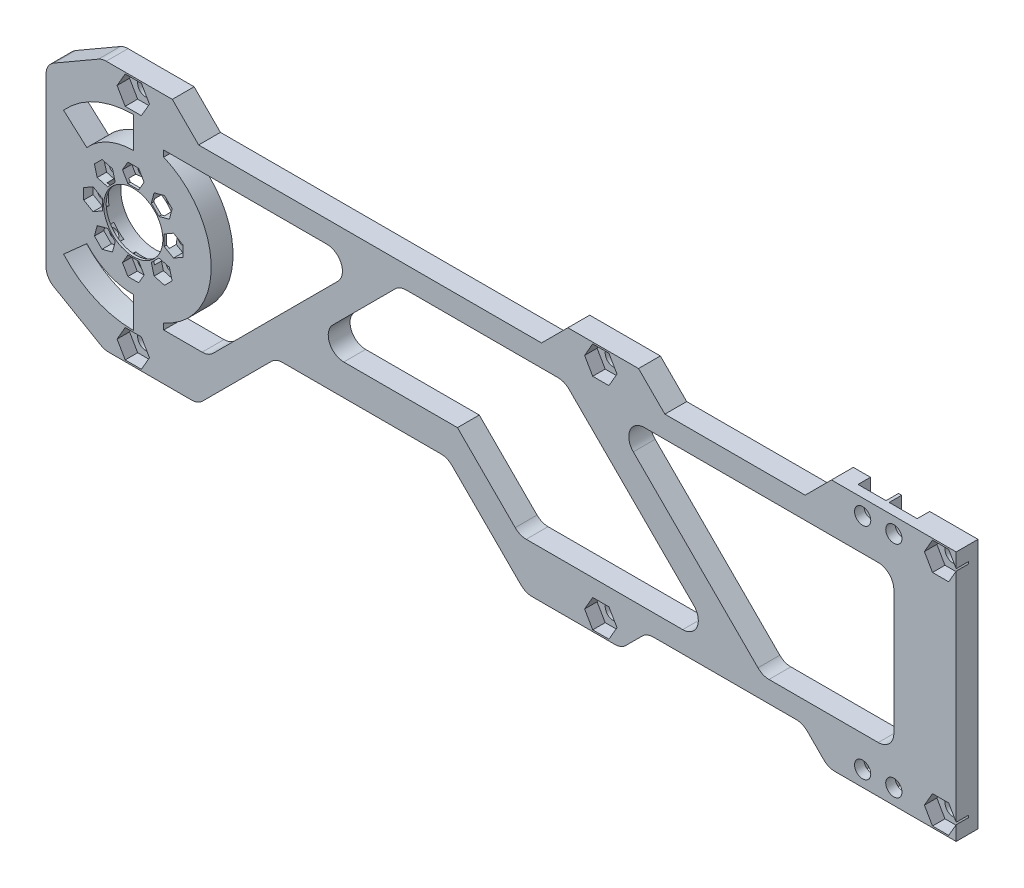
SolidWorks part; units mm, degrees
ref_plane "Front Plane" through (0, 0, 0) normal (0, 0, 1) x (1, 0, 0)
ref_plane "Top Plane" through (0, 0, 0) normal (0, 1, 0) x (1, 0, 0)
ref_plane "Right Plane" through (0, 0, 0) normal (1, 0, 0) x (0, 0, -1)
sketch "Sketch1" plane through (0, 0, 0) normal (0, 0, 1) x (1, 0, 0)
  line L0 (0, 0) -> (-274, 0)
  line L1 (-274, 0) -> (-299.9808, -15)
  line L2 (-299.9808, -15) -> (-299.9808, -65)
  line L3 (-299.9808, -65) -> (-273.2207, -80.4499)
  line L4 (-273.2207, -80.4499) -> (-243.2207, -80.4499)
  line L5 (-243.2207, -80.4499) -> (-218.1891, -55.4184)
  line L6 (-218.1891, -55.4184) -> (-163.1891, -55.4184)
  line L7 (-163.1891, -55.4184) -> (-138.1575, -80.4499)
  line L8 (-138.1575, -80.4499) -> (0, -80.4499)
  line L9 (0, -80.4499) -> (0, 0)
  dimension "D1" = 274
  dimension "D2" = 30
  dimension "D3" = 30
  dimension "D4" = 50
  dimension "D5" = 60
  dimension "D6" = 30
  dimension "D7" = 45
  dimension "D8" = 35.4
  dimension "D9" = 55
  dimension "D10" = 35.4
  dimension "D11" = 45
extrude "Boss-Extrude1" add sketch "Sketch1" along normal blind 7
sketch "Sketch2" plane through (0, 0, 7) normal (0, 0, 1) x (1, 0, 0)
  line L0 (-299.9808, -15) -> (-299.9808, -65) construction
  line L1 (-273.2207, -80.4499) -> (-243.2207, -80.4499) construction
  circle A0 centre (-263.9808, -40.4499) radius 9.5
  dimension "D1" = 36
  dimension "D2" = 40
  dimension "D3" = 19
extrude "Cut-Extrude1" cut sketch "Sketch2" against normal blind 7
sketch "Sketch3" plane through (0, 0, 7) normal (0, 0, 1) x (1, 0, 0)
  line L0 (-299.9808, -15) -> (-299.9808, -65) construction
  line L1 (-273.2207, -80.4499) -> (-243.2207, -80.4499) construction
  line L2 (0, -80.4499) -> (0, 0) construction
  line L3 (0, -40.225) -> (-214.1536, -40.225) construction
  circle A0 centre (-263.9808, -75.4499) radius 2.6
  circle A1 centre (-114, -75.4499) radius 2.6
  circle A2 centre (-30, -75.4499) radius 2.6
  circle A3 centre (-20, -75.4499) radius 2.6
  circle A4 centre (-5, -75.4499) radius 2.6
  circle A5 centre (-5, -5) radius 2.6
  circle A6 centre (-20, -5) radius 2.6
  circle A7 centre (-30, -5) radius 2.6
  circle A8 centre (-114, -5) radius 2.6
  circle A9 centre (-263.9808, -5) radius 2.6
  dimension "D1" = 5.2
  dimension "D2" = 36
  dimension "D3" = 5
  dimension "D4" = 5.2
  dimension "D5" = 5.2
  dimension "D6" = 5.2
  dimension "D7" = 5.2
  dimension "D8" = 114
  dimension "D9" = 10
  dimension "D10" = 20
  dimension "D11" = 5
extrude "Cut-Extrude2" cut sketch "Sketch3" against normal blind 7
sketch "Sketch5" plane through (0, 0, 0) normal (0, 0, -1) x (-1, 0, 0)
  line L0 (0, 0) -> (274, 0) construction
  line L2 (15.5, -5) -> (15.5, 0)
  line L3 (15.5, 0) -> (24.5, 0)
  line L4 (24.5, -5) -> (24.5, 0)
  line L5 (0, -40.225) -> (42.8271, -40.225) construction
  line L7 (25.5, -5) -> (25.5, 0)
  line L8 (25.5, 0) -> (34.5, 0)
  line L9 (34.5, -5) -> (34.5, 0)
  line L10 (0, -80.4499) -> (0, 0) construction
  line L11 (34.5, -75.4499) -> (34.5, -80.4499)
  line L12 (25.5, -80.4499) -> (34.5, -80.4499)
  line L13 (25.5, -75.4499) -> (25.5, -80.4499)
  line L14 (24.5, -75.4499) -> (24.5, -80.4499)
  line L15 (15.5, -80.4499) -> (24.5, -80.4499)
  line L16 (15.5, -75.4499) -> (15.5, -80.4499)
  arc A0 (15.5, -5) -> (24.5, -5) centre (20, -5) ccw
  arc A1 (25.5, -5) -> (34.5, -5) centre (30, -5) ccw
  arc A2 (25.5, -75.4499) -> (34.5, -75.4499) centre (30, -75.4499) cw
  arc A3 (15.5, -75.4499) -> (24.5, -75.4499) centre (20, -75.4499) cw
  dimension "D1" = 9
  dimension "D2" = 9
extrude "Cut-Extrude4" cut sketch "Sketch5" against normal blind 4
sketch "Sketch6" plane through (0, 0, 0) normal (0, 0, -1) x (-1, 0, 0)
  circle A0 centre (263.9808, -27.5499) radius 1.5
  circle A1 centre (263.9808, -40.4499) radius 9.5 construction
  circle A2 centre (273.1024, -31.3283) radius 1.5
  circle A3 centre (276.8808, -40.4499) radius 1.5
  circle A4 centre (273.1024, -49.5716) radius 1.5
  circle A5 centre (263.9808, -53.3499) radius 1.5
  circle A6 centre (254.8591, -49.5716) radius 1.5
  circle A7 centre (251.0808, -40.4499) radius 1.5
  circle A8 centre (254.8591, -31.3283) radius 1.5
  point P21 (263.9808, -40.4499)
  dimension "D1" = 12.9
  dimension "D2" = 3
  dimension "D3" = 8
extrude "Cut-Extrude5" cut sketch "Sketch6" against normal through all
sketch "Sketch8" plane through (0, 0, 0) normal (0, 0, -1) x (-1, 0, 0)
  circle A0 centre (263.9808, -40.4499) radius 11
  dimension "D1" = 22
extrude "Cut-Extrude8" cut sketch "Sketch8" against normal blind 6.2
sketch "Sketch10" plane through (0, 0, 7) normal (0, 0, 1) x (1, 0, 0)
  line L0 (0, -40.225) -> (-64.7485, -40.225) construction
  line L1 (-258.7846, -5) -> (-261.3827, -0.5)
  line L2 (-261.3827, -0.5) -> (-266.5788, -0.5)
  line L3 (-266.5788, -0.5) -> (-269.1769, -5)
  line L4 (-269.1769, -5) -> (-266.5788, -9.5)
  line L5 (-266.5788, -9.5) -> (-261.3827, -9.5)
  line L6 (-261.3827, -9.5) -> (-258.7846, -5)
  line L7 (-108.8038, -5) -> (-111.4019, -0.5)
  line L8 (-111.4019, -0.5) -> (-116.5981, -0.5)
  line L9 (-116.5981, -0.5) -> (-119.1962, -5)
  line L10 (-119.1962, -5) -> (-116.5981, -9.5)
  line L11 (-116.5981, -9.5) -> (-111.4019, -9.5)
  line L12 (-111.4019, -9.5) -> (-108.8038, -5)
  line L13 (0.1962, -5) -> (-2.4019, -0.5)
  line L14 (-2.4019, -0.5) -> (-7.5981, -0.5)
  line L15 (-7.5981, -0.5) -> (-10.1962, -5)
  line L16 (-10.1962, -5) -> (-7.5981, -9.5)
  line L17 (-7.5981, -9.5) -> (-2.4019, -9.5)
  line L18 (-2.4019, -9.5) -> (0.1962, -5)
  line L19 (0, -80.4499) -> (0, 0) construction
  line L20 (-2.4019, -70.9499) -> (0.1962, -75.4499)
  line L21 (-7.5981, -70.9499) -> (-2.4019, -70.9499)
  line L22 (-10.1962, -75.4499) -> (-7.5981, -70.9499)
  line L23 (-7.5981, -79.9499) -> (-10.1962, -75.4499)
  line L24 (-2.4019, -79.9499) -> (-7.5981, -79.9499)
  line L25 (0.1962, -75.4499) -> (-2.4019, -79.9499)
  line L26 (-111.4019, -70.9499) -> (-108.8038, -75.4499)
  line L27 (-116.5981, -70.9499) -> (-111.4019, -70.9499)
  line L28 (-119.1962, -75.4499) -> (-116.5981, -70.9499)
  line L29 (-116.5981, -79.9499) -> (-119.1962, -75.4499)
  line L30 (-111.4019, -79.9499) -> (-116.5981, -79.9499)
  line L31 (-108.8038, -75.4499) -> (-111.4019, -79.9499)
  line L32 (-261.3827, -70.9499) -> (-258.7846, -75.4499)
  line L33 (-266.5788, -70.9499) -> (-261.3827, -70.9499)
  line L34 (-269.1769, -75.4499) -> (-266.5788, -70.9499)
  line L35 (-266.5788, -79.9499) -> (-269.1769, -75.4499)
  line L36 (-261.3827, -79.9499) -> (-266.5788, -79.9499)
  line L37 (-258.7846, -75.4499) -> (-261.3827, -79.9499)
  circle A0 centre (-263.9808, -5) radius 4.5 construction
  circle A1 centre (-114, -5) radius 4.5 construction
  circle A2 centre (-5, -5) radius 4.5 construction
  circle A3 centre (-5, -75.4499) radius 4.5 construction
  circle A4 centre (-114, -75.4499) radius 4.5 construction
  circle A5 centre (-263.9808, -75.4499) radius 4.5 construction
  dimension "D1" = 9
  dimension "D2" = 9
  dimension "D3" = 9
extrude "Cut-Extrude10" cut sketch "Sketch10" against normal blind 4
sketch "Sketch11" plane through (0, 0, 7) normal (0, 0, 1) x (1, 0, 0)
  line L0 (-252.4096, -33.7778) -> (-251.513, -30.4317)
  line L1 (-260.5167, -27.5499) -> (-262.2487, -24.5499)
  line L2 (-262.2487, -24.5499) -> (-265.7128, -24.5499)
  line L3 (-265.7128, -24.5499) -> (-267.4449, -27.5499)
  line L4 (-267.4449, -27.5499) -> (-265.7128, -30.5499)
  line L5 (-265.7128, -30.5499) -> (-262.2487, -30.5499)
  line L6 (-262.2487, -30.5499) -> (-260.5167, -27.5499)
  line L7 (-251.513, -30.4317) -> (-253.9625, -27.9822)
  line L8 (-253.9625, -27.9822) -> (-257.3086, -28.8788)
  line L9 (-257.3086, -28.8788) -> (-258.2051, -32.2248)
  line L10 (-258.2051, -32.2248) -> (-255.7557, -34.6743)
  line L11 (-255.7557, -34.6743) -> (-252.4096, -33.7778)
  line L12 (-251.0808, -43.914) -> (-248.0808, -42.182)
  line L13 (-248.0808, -42.182) -> (-248.0808, -38.7179)
  line L14 (-248.0808, -38.7179) -> (-251.0808, -36.9858)
  line L15 (-251.0808, -36.9858) -> (-254.0808, -38.7179)
  line L16 (-254.0808, -38.7179) -> (-254.0808, -42.182)
  line L17 (-254.0808, -42.182) -> (-251.0808, -43.914)
  line L18 (-257.3086, -52.0211) -> (-253.9625, -52.9177)
  line L19 (-253.9625, -52.9177) -> (-251.513, -50.4682)
  line L20 (-251.513, -50.4682) -> (-252.4096, -47.1221)
  line L21 (-252.4096, -47.1221) -> (-255.7557, -46.2256)
  line L22 (-255.7557, -46.2256) -> (-258.2051, -48.675)
  line L23 (-258.2051, -48.675) -> (-257.3086, -52.0211)
  line L24 (-267.4449, -53.3499) -> (-265.7128, -56.3499)
  line L25 (-265.7128, -56.3499) -> (-262.2487, -56.3499)
  line L26 (-262.2487, -56.3499) -> (-260.5167, -53.3499)
  line L27 (-260.5167, -53.3499) -> (-262.2487, -50.3499)
  line L28 (-262.2487, -50.3499) -> (-265.7128, -50.3499)
  line L29 (-265.7128, -50.3499) -> (-267.4449, -53.3499)
  line L30 (-275.5519, -47.1221) -> (-276.4485, -50.4682)
  line L31 (-276.4485, -50.4682) -> (-273.999, -52.9177)
  line L32 (-273.999, -52.9177) -> (-270.6529, -52.0211)
  line L33 (-270.6529, -52.0211) -> (-269.7564, -48.675)
  line L34 (-269.7564, -48.675) -> (-272.2059, -46.2256)
  line L35 (-272.2059, -46.2256) -> (-275.5519, -47.1221)
  line L36 (-276.8808, -36.9858) -> (-279.8808, -38.7179)
  line L37 (-279.8808, -38.7179) -> (-279.8808, -42.182)
  line L38 (-279.8808, -42.182) -> (-276.8808, -43.914)
  line L39 (-276.8808, -43.914) -> (-273.8808, -42.182)
  line L40 (-273.8808, -42.182) -> (-273.8808, -38.7179)
  line L41 (-273.8808, -38.7179) -> (-276.8808, -36.9858)
  line L42 (-270.6529, -28.8788) -> (-273.999, -27.9822)
  line L43 (-273.999, -27.9822) -> (-276.4485, -30.4317)
  line L44 (-276.4485, -30.4317) -> (-275.5519, -33.7778)
  line L45 (-275.5519, -33.7778) -> (-272.2059, -34.6743)
  line L46 (-272.2059, -34.6743) -> (-269.7564, -32.2248)
  line L47 (-269.7564, -32.2248) -> (-270.6529, -28.8788)
  circle A0 centre (-263.9808, -27.5499) radius 3 construction
  point P54 (-263.9808, -40.4499)
  dimension "D1" = 6
  dimension "D2" = 8
extrude "Cut-Extrude11" cut sketch "Sketch11" against normal blind 3
sketch "Sketch12" plane through (0, 0, 0) normal (0, 0, -1) x (-1, 0, 0)
  line L0 (0, -80.4499) -> (0, 0) construction
  line L1 (20, -15.4499) -> (112.1103, -15.4499)
  line L2 (20, -15.4499) -> (20, -65.4499)
  line L3 (20, -65.4499) -> (62.1103, -65.4499)
  line L5 (20, -15.4499) -> (140, -65.4499) construction
  line L6 (20, -65.4499) -> (140, -15.4499) construction
  line L7 (140, -65.4499) -> (159.9902, -45.4598)
  line L8 (159.9902, -45.4598) -> (208.5159, -45.4598)
  line L9 (219.8296, -45.4598) -> (239.8198, -65.4499)
  line L10 (239.8198, -65.4499) -> (254.2144, -65.4499)
  line L11 (140, -15.4499) -> (178.5061, -15.4499)
  line L12 (62.1103, -65.4499) -> (112.1103, -15.4499)
  line L14 (125.6517, -15.4499) -> (75.6517, -65.4499)
  line L16 (75.6517, -65.4499) -> (140, -65.4499)
  line L17 (125.6517, -15.4499) -> (140, -15.4499)
  line L18 (219.8296, -45.4598) -> (189.8198, -15.4499)
  line L20 (178.5061, -15.4499) -> (208.5159, -45.4598)
  line L22 (189.8198, -15.4499) -> (254.2144, -15.4499)
  line L23 (254.2144, -15.4499) -> (254.2144, -17.4365)
  line L24 (254.2144, -63.4634) -> (254.2144, -65.4499)
  arc A1 (254.2144, -17.4365) -> (254.2144, -63.4634) centre (263.9808, -40.4499) ccw
  point P0 (80, -40.4499)
  dimension "D1" = 80
  dimension "D2" = 120
  dimension "D3" = 50
  dimension "D5" = 8
extrude "Cut-Extrude13" cut sketch "Sketch12" against normal through all
fillet "Fillet1" radius 5 11 edges at (-239.8198, -65.4499, 3.5) (-189.8198, -15.4499, 3.5) (-178.5061, -15.4499, 3.5) (-208.5159, -45.4598, 3.5) (-125.6517, -15.4499, 3.5) (-140, -65.4499, 3.5) (-75.6517, -65.4499, 3.5) (-112.1103, -15.4499, 3.5) (-62.1103, -65.4499, 3.5) (-20, -15.4499, 3.5) (-20, -65.4499, 3.5)
sketch "Sketch13" plane through (0, 0, 0) normal (0, 0, -1) x (-1, 0, 0)
  line L0 (40, 0) -> (48.4499, -8.4499)
  line L1 (34.5, 0) -> (274, 0) construction
  line L2 (48.4499, -8.4499) -> (93.4499, -8.4499)
  line L3 (0, -80.4499) -> (0, 0) construction
  line L4 (93.4499, -8.4499) -> (101.8999, 0)
  line L5 (40, 0) -> (101.8999, 0)
  line L6 (124.5668, 0) -> (133.0167, -8.4499)
  line L7 (133.0167, -8.4499) -> (243.0167, -8.4499)
  line L8 (243.0167, -8.4499) -> (251.4666, 0)
  line L9 (251.4666, 0) -> (124.5668, 0)
  line L10 (263.9808, -60.4499) -> (263.9808, -70.4499)
  line L11 (263.9808, -20.4499) -> (263.9808, -10.4499)
  line L12 (176.435, -15.4499) -> (127.7227, -15.4499) construction
  line L13 (100.0393, -15.4499) -> (25, -15.4499) construction
  line L14 (278.8879, -27.1166) -> (286.3414, -20.4499)
  line L15 (278.8879, -53.7833) -> (286.3414, -60.4499)
  arc A0 (263.9808, -70.4499) -> (286.3414, -60.4499) centre (263.9808, -40.4499) ccw
  arc A1 (263.9808, -60.4499) -> (278.8879, -53.7833) centre (263.9808, -40.4499) ccw
  arc A2 (278.8879, -27.1166) -> (263.9808, -20.4499) centre (263.9808, -40.4499) ccw
  arc A3 (286.3414, -20.4499) -> (263.9808, -10.4499) centre (263.9808, -40.4499) ccw
  dimension "D4" = 60
  dimension "D5" = 40
  dimension "D1" = 45
  dimension "D2" = 40
  dimension "D3" = 110
  dimension "D6" = 7
  dimension "D7" = 7
  dimension "D8" = 45
  dimension "D9" = 45
extrude "Cut-Extrude15" cut sketch "Sketch13" against normal through all
sketch "Sketch14" plane through (0, 0, 0) normal (0, 0, -1) x (-1, 0, 0)
  line L0 (291.9808, -69.6188) -> (291.9808, -10.3812)
  line L1 (299.9808, -65) -> (273.2207, -80.4499) construction
  line L2 (274, 0) -> (299.9808, -15) construction
  line L3 (299.9808, -15) -> (299.9808, -65) construction
  line L4 (291.9808, -10.3812) -> (299.9808, -15)
  line L5 (299.9808, -15) -> (299.9808, -65)
  line L6 (299.9808, -65) -> (291.9808, -69.6188)
  dimension "D1" = 8
extrude "Cut-Extrude16" cut sketch "Sketch14" against normal through all
sketch "Sketch15" plane through (0, 0, 0) normal (0, 0, -1) x (-1, 0, 0)
  line L0 (41.0037, -80.4499) -> (49.2214, -72.2322)
  line L1 (138.1575, -80.4499) -> (34.5, -80.4499) construction
  line L2 (49.2214, -72.2322) -> (99.2214, -72.2322)
  line L3 (99.2214, -72.2322) -> (107.4391, -80.4499)
  line L4 (107.4391, -80.4499) -> (41.0037, -80.4499)
  dimension "D1" = 50
extrude "Cut-Extrude17" cut sketch "Sketch15" against normal through all
fillet "Fillet4" radius 5 4 edges at (-274, 0, 3.5) (-273.2207, -80.4499, 3.5) (-291.9808, -69.6188, 3.5) (-291.9808, -10.3812, 3.5)
fillet "Fillet5" radius 5 8 edges at (-41.0037, -80.4499, 3.5) (-49.2214, -72.2322, 3.5) (-99.2214, -72.2322, 3.5) (-107.4391, -80.4499, 3.5) (-243.2207, -80.4499, 3.5) (-138.1575, -80.4499, 3.5) (-218.1891, -55.4184, 3.5) (-163.1891, -55.4184, 3.5)
